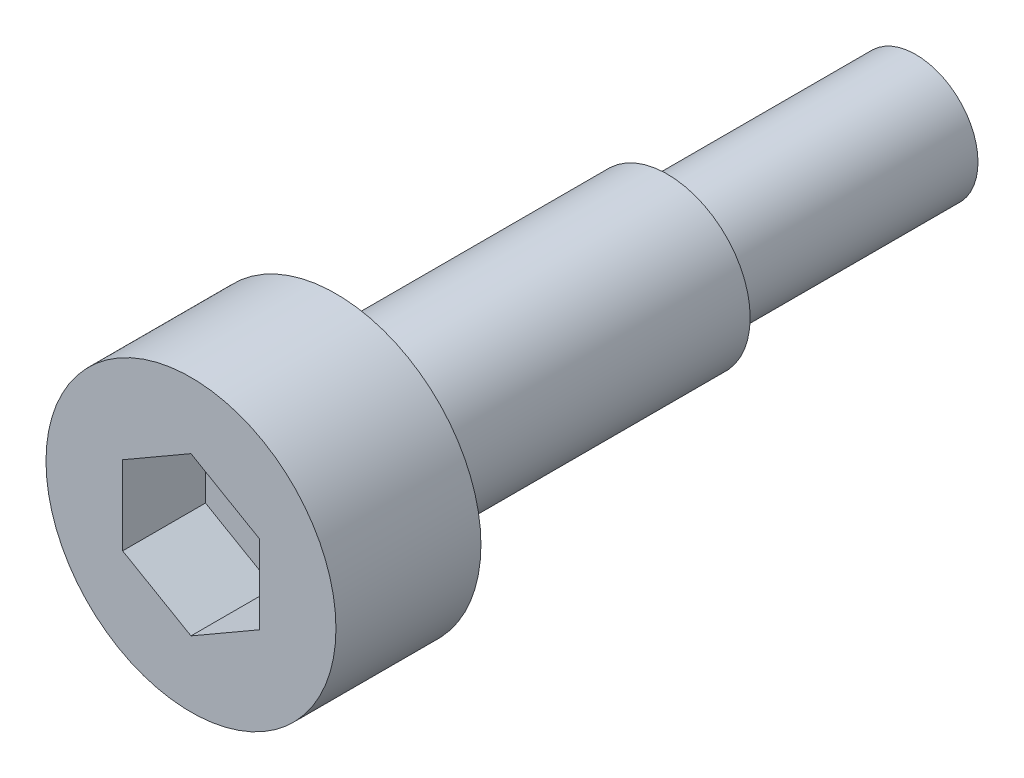
SolidWorks part; units mm, degrees
ref_plane "前视基准面" through (0, 0, 0) normal (0, 0, 1) x (1, 0, 0)
ref_plane "上视基准面" through (0, 0, 0) normal (0, 1, 0) x (1, 0, 0)
ref_plane "右视基准面" through (0, 0, 0) normal (1, 0, 0) x (0, 0, -1)
sketch "草图1" plane through (0, 0, 0) normal (0, 0, 1) x (1, 0, 0)
  circle A0 centre (0, 0) radius 1.5
  dimension "D1" = 3
extrude "凸台-拉伸1" add sketch "草图1" along normal blind 6
cosmetic thread "装饰螺纹线1" parameters "D2"=2.459
cosmetic thread "装饰螺纹线2" parameters "D2"=2.459
sketch "草图2" plane through (0, 0, 6) normal (0, 0, 1) x (1, 0, 0)
  circle A0 centre (0, 0) radius 2
  dimension "D1" = 4
extrude "凸台-拉伸2" add sketch "草图2" along normal blind 8
sketch "草图3" plane through (0, 0, 14) normal (0, 0, 1) x (1, 0, 0)
  circle A0 centre (0, 0) radius 3.5
  dimension "D1" = 7
extrude "凸台-拉伸3" add sketch "草图3" along normal blind 3.5
sketch "草图4" plane through (0, 0, 17.5) normal (0, 0, 1) x (1, 0, 0)
  line L0 (0, 4.0991) -> (0, -4.5705) construction
  line L1 (0, 1.9053) -> (-1.65, 0.9526)
  line L2 (-1.65, 0.9526) -> (-1.65, -0.9526)
  line L3 (-1.65, -0.9526) -> (0, -1.9053)
  line L4 (0, -1.9053) -> (1.65, -0.9526)
  line L5 (1.65, -0.9526) -> (1.65, 0.9526)
  line L6 (1.65, 0.9526) -> (0, 1.9053)
  circle A0 centre (0, 0) radius 1.65 construction
  dimension "D1" = 3.3
extrude "切除-拉伸1" cut sketch "草图4" against normal blind 2
